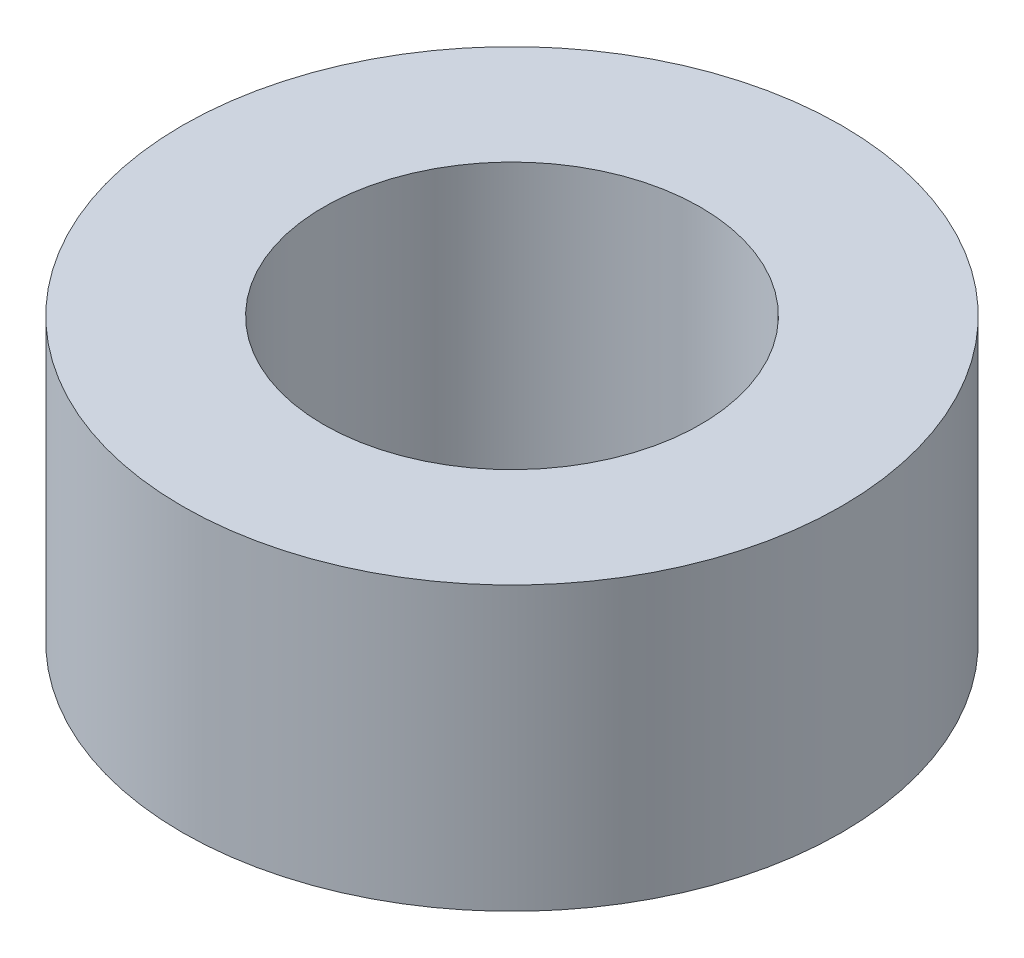
SolidWorks part; units mm, degrees
ref_plane "Front Plane" through (0, 0, 0) normal (0, 0, 1) x (1, 0, 0)
ref_plane "Top Plane" through (0, 0, 0) normal (0, 1, 0) x (1, 0, 0)
ref_plane "Right Plane" through (0, 0, 0) normal (1, 0, 0) x (0, 0, -1)
sketch "Sketch1" plane through (0, 0, 0) normal (0, 1, 0) x (1, 0, 0)
  circle A0 centre (0, 0) radius 2
  circle A1 centre (0, 0) radius 3.5
  dimension "D1" = 4
  dimension "D2" = 7
extrude "Boss-Extrude1" add sketch "Sketch1" along normal blind 3
